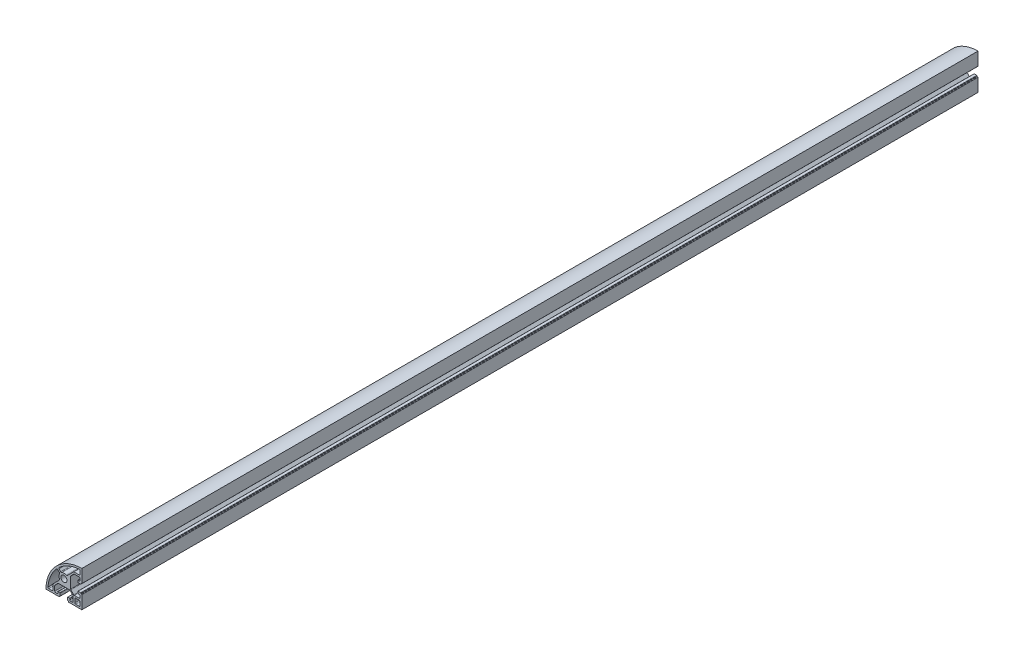
SolidWorks part; units mm, degrees
material "6063 T5"
ref_plane "Спереди" through (0, 0, 0) normal (0, 0, 1) x (1, 0, 0)
ref_plane "Сверху" through (0, 0, 0) normal (0, 1, 0) x (1, 0, 0)
ref_plane "Справа" through (0, 0, 0) normal (1, 0, 0) x (0, 0, -1)
sketch "Эскиз1" plane through (0, 0, 0) normal (0, 0, 1) x (1, 0, 0)
  line L0 (10.25, -20) -> (20, -20)
  line L1 (20, -20) -> (20, -10.25)
  line L2 (20, 10.25) -> (20, 20)
  line L3 (-20, -20) -> (-10.25, -20)
  line L6 (-16.8782, -18) -> (-13.2473, -18)
  line L7 (-12.2473, -17) -> (-12.2473, -11)
  line L8 (-19.9864, 20.9431) -> (20.0136, 20.9431) construction
  line L9 (-20.0289, 20.8455) -> (19.9711, 20.8455) construction
  line L10 (13.2, -12.2) -> (17, -12.2)
  line L11 (12.2, -13.2) -> (12.2, -17)
  line L12 (13.2, -18) -> (17, -18)
  line L13 (18, -13.2) -> (18, -17)
  line L15 (-5.023, -3.7757) -> (-12.2473, -11)
  line L16 (0, 0) -> (-32.9488, 32.9488) construction
  line L17 (-6.8318, 5.4176) -> (-5.0803, 3.6661)
  line L18 (-5.4176, 6.8318) -> (-3.6661, 5.0803)
  line L19 (18, 16.8782) -> (18, 13.2473)
  line L20 (17, 12.2473) -> (11, 12.2473)
  line L21 (3.7757, 5.023) -> (11, 12.2473)
  arc A0 (-20, -20) -> (20, 20) centre (20, -20) cw
  circle A1 centre (0, 0) radius 3.4
  arc A2 (-17.8749, -16.9189) -> (-8.2832, 5.3783) centre (20, -20) cw
  arc A4 (12.2, -17) -> (13.2, -18) centre (13.2, -17) ccw
  arc A5 (17, -18) -> (18, -17) centre (17, -17) ccw
  arc A6 (17, -12.2) -> (18, -13.2) centre (17, -13.2) cw
  arc A7 (13.2, -12.2) -> (12.2, -13.2) centre (13.2, -13.2) ccw
  arc A8 (-4.8971, 2.5038) -> (-4.8485, -2.5965) centre (0, 0) ccw
  arc A9 (-4.8485, -2.5965) -> (-5.023, -3.7757) centre (-5.7301, -3.0686) cw
  arc A13 (-13.2473, -18) -> (-12.2473, -17) centre (-13.2473, -17) ccw
  arc A14 (-17.8749, -16.9189) -> (-16.8782, -18) centre (-16.8782, -17) ccw
  arc A16 (-4.8971, 2.5038) -> (-5.0803, 3.6661) centre (-5.7874, 2.959) ccw
  arc A17 (-6.8318, 5.4176) -> (-8.2832, 5.3783) centre (-7.5389, 4.7105) ccw
  arc A18 (2.5965, 4.8485) -> (3.7757, 5.023) centre (3.0686, 5.7301) ccw
  arc A19 (-2.5038, 4.8971) -> (2.5965, 4.8485) centre (0, 0) cw
  arc A20 (-2.5038, 4.8971) -> (-3.6661, 5.0803) centre (-2.959, 5.7874) cw
  arc A21 (-5.4176, 6.8318) -> (-5.3783, 8.2832) centre (-4.7105, 7.5389) cw
  arc A22 (16.9189, 17.8749) -> (-5.3783, 8.2832) centre (20, -20) ccw
  arc A23 (16.9189, 17.8749) -> (18, 16.8782) centre (17, 16.8782) cw
  arc A24 (18, 13.2473) -> (17, 12.2473) centre (17, 13.2473) cw
  point P28 (18, -12.2)
  point P31 (12.2, -12.2)
  point P48 (-12.2473, -18)
  point P51 (-17.9473, -18)
  line B0 (20, -10.25) -> (20, -5.4)
  line B1 (19.7, -5.1) -> (19.3, -5.1)
  line B2 (19, -4.8) -> (19, -4.4)
  line B3 (18.7, -4.1) -> (15.8, -4.1)
  line B4 (15.5, -4.4) -> (15.5, -6.3)
  line B5 (15.8, -6.6) -> (17, -6.6)
  line B6 (18, -7.6) -> (18, -9.25)
  line B7 (17, -10.25) -> (11.6642, -10.25)
  line B8 (10.9571, -9.9571) -> (7.7929, -6.7929)
  line B9 (7.5, -6.0858) -> (7.5, 6.0858)
  line B10 (7.5, 0) -> (20, 0) construction
  line B11 (10.9571, 9.9571) -> (7.7929, 6.7929)
  line B12 (17, 10.25) -> (11.6642, 10.25)
  line B13 (18, 7.6) -> (18, 9.25)
  line B14 (15.8, 6.6) -> (17, 6.6)
  line B15 (15.5, 4.4) -> (15.5, 6.3)
  line B16 (18.7, 4.1) -> (15.8, 4.1)
  line B17 (19, 4.8) -> (19, 4.4)
  line B18 (19.7, 5.1) -> (19.3, 5.1)
  line B19 (20, 10.25) -> (20, 5.4)
  arc B20 (15.5, -6.3) -> (15.8, -6.6) centre (15.8, -6.3) ccw
  arc B21 (15.8, -4.1) -> (15.5, -4.4) centre (15.8, -4.4) ccw
  arc B22 (19, -4.4) -> (18.7, -4.1) centre (18.7, -4.4) ccw
  arc B23 (19.3, -5.1) -> (19, -4.8) centre (19.3, -4.8) cw
  arc B24 (20, -5.4) -> (19.7, -5.1) centre (19.7, -5.4) ccw
  arc B25 (7.7929, -6.7929) -> (7.5, -6.0858) centre (8.5, -6.0858) cw
  arc B26 (11.6642, -10.25) -> (10.9571, -9.9571) centre (11.6642, -9.25) cw
  arc B27 (18, -9.25) -> (17, -10.25) centre (17, -9.25) cw
  arc B28 (17, -6.6) -> (18, -7.6) centre (17, -7.6) cw
  arc B29 (17, 6.6) -> (18, 7.6) centre (17, 7.6) ccw
  arc B30 (18, 9.25) -> (17, 10.25) centre (17, 9.25) ccw
  arc B31 (11.6642, 10.25) -> (10.9571, 9.9571) centre (11.6642, 9.25) ccw
  arc B32 (7.7929, 6.7929) -> (7.5, 6.0858) centre (8.5, 6.0858) ccw
  arc B33 (20, 5.4) -> (19.7, 5.1) centre (19.7, 5.4) cw
  arc B34 (19.3, 5.1) -> (19, 4.8) centre (19.3, 4.8) ccw
  arc B35 (19, 4.4) -> (18.7, 4.1) centre (18.7, 4.4) cw
  arc B36 (15.8, 4.1) -> (15.5, 4.4) centre (15.8, 4.4) cw
  arc B37 (15.5, 6.3) -> (15.8, 6.6) centre (15.8, 6.3) cw
  line B38 (-10.25, -20) -> (-5.4, -20)
  line B39 (-5.1, -19.7) -> (-5.1, -19.3)
  line B40 (-4.8, -19) -> (-4.4, -19)
  line B41 (-4.1, -18.7) -> (-4.1, -15.8)
  line B42 (-4.4, -15.5) -> (-6.3, -15.5)
  line B43 (-6.6, -15.8) -> (-6.6, -17)
  line B44 (-7.6, -18) -> (-9.25, -18)
  line B45 (-10.25, -17) -> (-10.25, -11.6642)
  line B46 (-9.9571, -10.9571) -> (-6.7929, -7.7929)
  line B47 (-6.0858, -7.5) -> (6.0858, -7.5)
  line B48 (0, -7.5) -> (0, -20) construction
  line B49 (9.9571, -10.9571) -> (6.7929, -7.7929)
  line B50 (10.25, -17) -> (10.25, -11.6642)
  line B51 (7.6, -18) -> (9.25, -18)
  line B52 (6.6, -15.8) -> (6.6, -17)
  line B53 (4.4, -15.5) -> (6.3, -15.5)
  line B54 (4.1, -18.7) -> (4.1, -15.8)
  line B55 (4.8, -19) -> (4.4, -19)
  line B56 (5.1, -19.7) -> (5.1, -19.3)
  line B57 (10.25, -20) -> (5.4, -20)
  arc B58 (-6.3, -15.5) -> (-6.6, -15.8) centre (-6.3, -15.8) ccw
  arc B59 (-4.1, -15.8) -> (-4.4, -15.5) centre (-4.4, -15.8) ccw
  arc B60 (-4.4, -19) -> (-4.1, -18.7) centre (-4.4, -18.7) ccw
  arc B61 (-5.1, -19.3) -> (-4.8, -19) centre (-4.8, -19.3) cw
  arc B62 (-5.4, -20) -> (-5.1, -19.7) centre (-5.4, -19.7) ccw
  arc B63 (-6.7929, -7.7929) -> (-6.0858, -7.5) centre (-6.0858, -8.5) cw
  arc B64 (-10.25, -11.6642) -> (-9.9571, -10.9571) centre (-9.25, -11.6642) cw
  arc B65 (-9.25, -18) -> (-10.25, -17) centre (-9.25, -17) cw
  arc B66 (-6.6, -17) -> (-7.6, -18) centre (-7.6, -17) cw
  arc B67 (6.6, -17) -> (7.6, -18) centre (7.6, -17) ccw
  arc B68 (9.25, -18) -> (10.25, -17) centre (9.25, -17) ccw
  arc B69 (10.25, -11.6642) -> (9.9571, -10.9571) centre (9.25, -11.6642) ccw
  arc B70 (6.7929, -7.7929) -> (6.0858, -7.5) centre (6.0858, -8.5) ccw
  arc B71 (5.4, -20) -> (5.1, -19.7) centre (5.4, -19.7) cw
  arc B72 (5.1, -19.3) -> (4.8, -19) centre (4.8, -19.3) ccw
  arc B73 (4.4, -19) -> (4.1, -18.7) centre (4.4, -18.7) cw
  arc B74 (4.1, -15.8) -> (4.4, -15.5) centre (4.4, -15.8) cw
  arc B75 (6.3, -15.5) -> (6.6, -15.8) centre (6.3, -15.8) cw
  dimension "D3" = 40
  dimension "D4" = 6.8
  dimension "D9" = 1
  dimension "D10" = 1
  dimension "D13" = 38
  dimension "D15" = 1
  dimension "D16" = 45
  dimension "D11" = 5.5
  dimension "D19" = 45
  dimension "D20" = 1
  dimension "D1" = 20
  dimension "D2" = 20
  dimension "D5" = 40
  dimension "D6" = 2
  dimension "D7" = 2
  dimension "D8" = 5.8
  dimension "D12" = 2
  dimension "D14" = 5.7
  dimension "D17" = 40
  dimension "D18" = 7
sketch_block_instance "8B(20,5PL)-2"
sketch_block "8B(20,5PL)" parameters "D7"=0.3, "D8"=1, "D1"=12.5, "D2"=4.5, "D3"=8.2, "D4"=20.5, "D5"=10.2, "D6"=135, "D9"=0.4, "D10"=1.65, "D11"=10.7577, "D12"=1.2
sketch_block_instance "8B(20,5PL)-3"
extrude "Бобышка-Вытянуть1" add sketch "Эскиз1" along normal blind 1000
